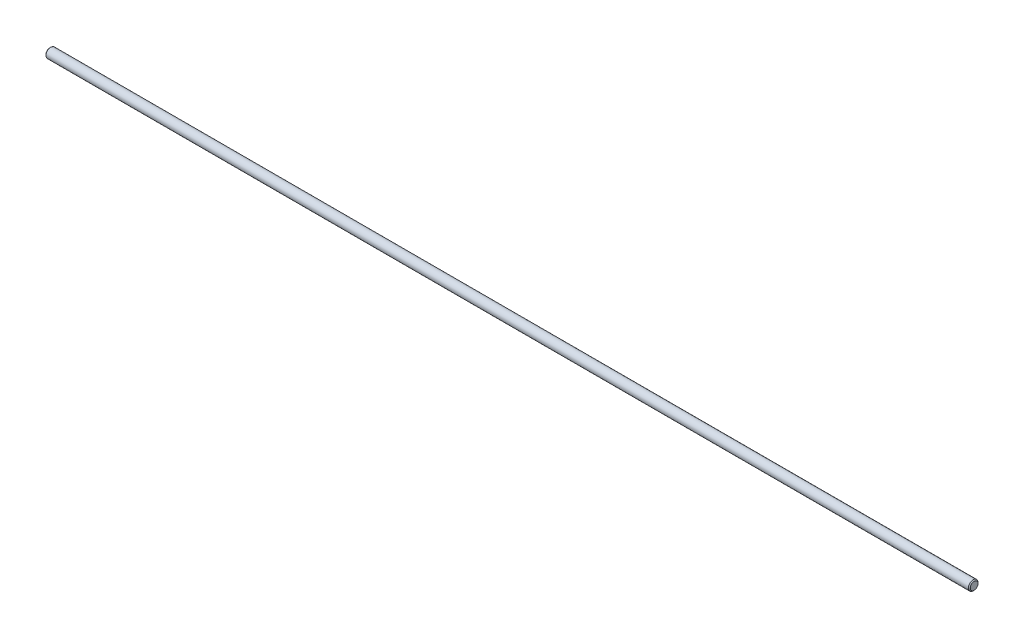
SolidWorks part; units mm, degrees
ref_plane "Front" through (0, 0, 0) normal (0, 0, 1) x (1, 0, 0)
ref_plane "Top" through (0, 0, 0) normal (0, 1, 0) x (1, 0, 0)
ref_plane "Right" through (0, 0, 0) normal (1, 0, 0) x (0, 0, -1)
sketch "Sketch1" plane through (0, 0, 0) normal (0, 0, 1) x (1, 0, 0)
  line L0 (-304.8, 0) -> (304.8, 0) construction
  line L1 (304.8, 3.175) -> (304.8, -3.175) construction
  line L2 (-304.8, 3.175) -> (-304.8, -3.175) construction
  dimension "Length" = 609.6
  dimension "Diameter" = 6.35
sketch "Sketch2" plane through (0, 0, 0) normal (1, 0, 0) x (0, 0, -1)
  circle A0 centre (0, 0) radius 3.175
extrude "Extrude1" add sketch "Sketch2" against normal up to vertex (304.8 mm away) and the other way up to vertex (304.8 mm away) up to point (-304.8, 3.175, 0) other way up to point (304.8, 3.175, 0)
chamfer "Chamfer1" distance 0.635 angle 45 2 edges at (304.8, 0, -3.175) (-304.8, 0, -3.175)
equation "\"D1@Chamfer1\" = \"Diameter@Sketch1\"*.1"
